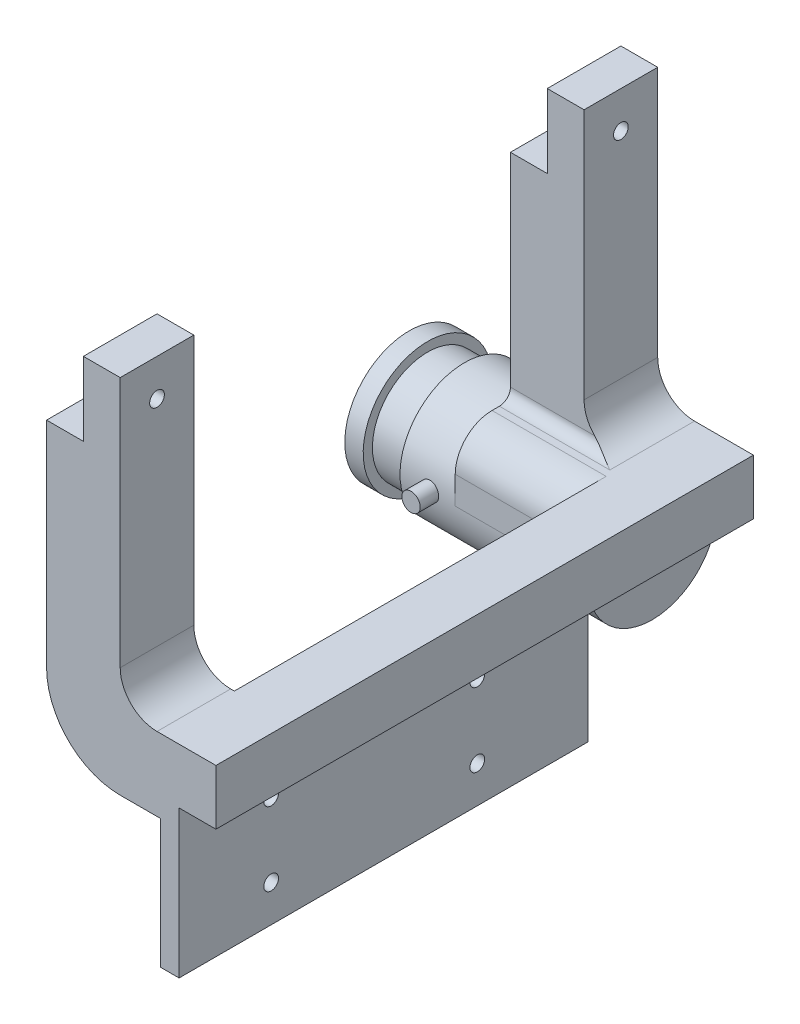
SolidWorks part; units mm, degrees
ref_plane "Front Plane" through (0, 0, 0) normal (0, 0, 1) x (1, 0, 0)
ref_plane "Top Plane" through (0, 0, 0) normal (0, 1, 0) x (1, 0, 0)
ref_plane "Right Plane" through (0, 0, 0) normal (1, 0, 0) x (0, 0, -1)
sketch "Sketch4" plane through (0, 0, 0) normal (1, 0, 0) x (0, 0, -1)
  line L0 (0, 10) -> (-10, 10)
  line L1 (0, 0) -> (126, 0)
  line L2 (0, 0) -> (0, 10)
  line L3 (0, 10) -> (126, 10) construction
  line L4 (126, 0) -> (126, 10)
  line L5 (-10, 10) -> (-10, 25)
  line L6 (-10, 25) -> (136, 25)
  line L7 (136, 25) -> (136, 10)
  line L8 (136, 10) -> (126, 10)
  dimension "D1" = 10
  dimension "D2" = 126
  dimension "D3" = 10
  dimension "D4" = 10
  dimension "D5" = 15
extrude "Boss-Extrude3" add sketch "Sketch4" along normal blind 10
sketch "Sketch8" plane through (0, 0, 0) normal (-1, 0, 0) x (0, 0, 1)
  line L1 (-136, 25) -> (10, 25)
  line L2 (-136, 25) -> (-136, 10)
  line L3 (-136, 10) -> (10, 10)
  line L4 (10, 25) -> (10, 10)
extrude "Boss-Extrude6" add sketch "Sketch8" along normal blind 5
sketch "Sketch9" plane through (0, 10, 0) normal (0, -1, 0) x (1, 0, 0)
  line L0 (10, -136) -> (-5, -136) construction
  line L1 (-5, 10) -> (0, 10)
  line L2 (-5, 10) -> (-5, -136)
  line L3 (-5, -136) -> (0, -136)
  line L4 (0, 10) -> (0, -136)
extrude "Boss-Extrude7" add sketch "Sketch9" along normal blind 20
sketch "Sketch10" plane through (0, 0, 0) normal (1, 0, 0) x (0, 0, -1)
  line L0 (0, 0) -> (0, -10) construction
  line L1 (136, -10) -> (-10, -10) construction
  line L2 (126, 0) -> (126, -10) construction
  line L3 (43, 0) -> (43, -10) construction
  line L5 (-10, -10) -> (-10, 10) construction
  circle A0 centre (15, -5) radius 2
  circle A1 centre (71, -5) radius 2
  dimension "D2" = 4
  dimension "D1" = 15
  dimension "D3" = 53
extrude "Cut-Extrude2" [suppressed] cut sketch "Sketch10" against normal blind 20
sketch "Sketch5" plane through (10, 0, 0) normal (1, 0, 0) x (0, 0, -1)
  line L0 (266, 95.52) -> (266, 25) construction
  line L1 (136, 10) -> (266, 10)
  line L2 (136, 10) -> (136, 25)
  line L3 (136, 25) -> (261, 25)
  line L4 (266, 10) -> (266, 25) construction
  line L5 (266, 10) -> (276, 10)
  line L6 (266, 10) -> (266, 95.52) construction
  line L7 (266, 95.52) -> (281, 95.52) construction
  line L8 (281, 10) -> (281, 95.52) construction
  line L9 (266, 84.1664) -> (266, 30)
  line L10 (281, 84.1664) -> (281, 15)
  circle A0 centre (273.5, 102.02) radius 6.5
  arc A1 (263, 91.3079) -> (284, 91.3079) centre (273.5, 102.02) cw
  arc A2 (284, 91.3079) -> (281, 84.1664) centre (291, 84.1664) ccw
  arc A3 (263, 91.3079) -> (266, 84.1664) centre (256, 84.1664) cw
  arc A4 (276, 10) -> (281, 15) centre (276, 15) ccw
  arc A5 (261, 25) -> (266, 30) centre (261, 30) ccw
  point P14 (281, 89.0296)
  point P17 (266, 89.0296)
  dimension "D5" = 13
  dimension "D6" = 15
  dimension "D7" = 10
  dimension "D8" = 5
  dimension "D1" = 130
  dimension "D2" = 15
  dimension "D3" = 15
  dimension "D4" = 85.52
  dimension "D9" = 7.5
extrude "Boss-Extrude4" [suppressed] add sketch "Sketch5" against normal blind 15
sketch "Sketch6" [suppressed] plane through (-5, 0, 0) normal (-1, 0, 0) x (0, 0, 1)
  circle A0 centre (-273.5, 102.02) radius 6.5
  circle A1 centre (-273.5, 102.02) radius 15
extrude "Boss-Extrude5" [suppressed] add sketch "Sketch6" along normal blind 50
ref_plane "Plane2" [suppressed] through (0, 0, -288.5) normal (0, 0, -1) x (-1, 0, 0)
ref_plane "Plane3" [suppressed] through (0, 0, -258.5) normal (0, 0, 1) x (1, 0, 0)
sketch "Sketch7" [suppressed] plane through (0, 0, -288.5) normal (0, 0, -1) x (-1, 0, 0)
  line L0 (-10, 117.02) -> (-10, 91.3079) construction
  circle A0 centre (20, 102.02) radius 2
  circle A1 centre (0, 102.02) radius 2
  dimension "D1" = 4
  dimension "D2" = 4
  dimension "D3" = 10
  dimension "D4" = 20
extrude "Cut-Extrude1" [suppressed] cut sketch "Sketch7" against normal blind 50
sketch "Sketch13" [suppressed] plane through (-5, 0, 0) normal (-1, 0, 0) x (0, 0, 1)
  line L0 (-196, 25) -> (-196, 10) construction
  line L1 (-136, 10) -> (-276, 10) construction
  line L2 (-136, 25) -> (-136, 10) construction
  circle A0 centre (-190, 17.5) radius 2
  circle A1 centre (-142, 17.5) radius 2
  dimension "D2" = 4
  dimension "D3" = 4
  dimension "D1" = 6
  dimension "D4" = 6
extrude "Cut-Extrude3" [suppressed] cut sketch "Sketch13" against normal blind 20
sketch "Sketch12" [suppressed] plane through (0, 25, 0) normal (0, 1, 0) x (1, 0, 0)
  line L0 (-5, 136) -> (10, 136) construction
  line L1 (-5, -10) -> (-5, 261) construction
  line L2 (10, 261) -> (10, -10) construction
  line L3 (10, -10) -> (-5, -10) construction
  line L4 (-5, 196) -> (10, 196) construction
  line L5 (2.5, 196) -> (2.5, 136)
  line L6 (2.5, 196) -> (-5, 196)
  line L7 (2.5, 136) -> (10, 136)
  dimension "D1" = 146
  dimension "D2" = 60
split "Split2" [suppressed] bodies to split 112
sketch "Sketch14" plane through (0, 0, 10) normal (0, 0, 1) x (1, 0, 0)
  line L0 (-5, 25) -> (-6, 25)
  line L1 (-16, 35) -> (-16, 83.24)
  line L2 (-16, 83.24) -> (-36, 83.24) construction
  line L3 (-36, 83.24) -> (-36, 25)
  line L4 (-16, 5) -> (-5, 5)
  line L5 (-5, -10) -> (-5, 25) construction
  line L6 (-5, 5) -> (-5, 25)
  line L8 (10, 25) -> (-5, 25) construction
  line L9 (-36, 83.24) -> (-36, 93.24)
  line L10 (-36, 93.24) -> (-36, 103.24)
  line L11 (-36, 103.24) -> (-16, 103.24)
  line L12 (-16, 103.24) -> (-16, 83.24)
  arc A0 (-6, 25) -> (-16, 35) centre (-6, 35) cw
  arc A1 (-36, 25) -> (-16, 5) centre (-16, 25) ccw
  point P16 (-16, 25)
  point P19 (-36, 5)
  dimension "D7" = 10
  dimension "D8" = 20
  dimension "D1" = 20
  dimension "D2" = 20
  dimension "D3" = 78.24
  dimension "D4" = 10
  dimension "D5" = 10
  dimension "D6" = 11
ref_plane "Plane4" through (0, 0, -63) normal (0, 0, 1) x (1, 0, 0)
extrude "Boss-Extrude8" add sketch "Sketch14" against normal blind 20
sketch "Sketch17" plane through (-36, 0, 0) normal (-1, 0, 0) x (0, 0, 1)
  line L0 (10, 103.24) -> (10, 25) construction
  line L1 (-10, 103.24) -> (10, 103.24)
  line L2 (-10, 103.24) -> (-10, 83.24)
  line L3 (-10, 83.24) -> (10, 83.24)
  line L4 (10, 103.24) -> (10, 83.24)
  dimension "D1" = 20
extrude "Cut-Extrude4" cut sketch "Sketch17" against normal blind 10
sketch "Sketch18" plane through (-26, 0, 0) normal (-1, 0, 0) x (0, 0, 1)
  line L0 (10, 103.24) -> (-10, 103.24) construction
  circle A0 centre (0, 93.24) radius 2
  dimension "D1" = 4
  dimension "D2" = 10
extrude "Cut-Extrude5" cut sketch "Sketch18" against normal up to next (10 mm away)
mirror "Mirror2" about plane through (0, 0, -63) normal (0, 0, 1) of "Cut-Extrude5", "Cut-Extrude4", "Boss-Extrude8"
sketch "Sketch20" plane through (-36, 0, 0) normal (-1, 0, 0) x (0, 0, 1)
  line L0 (10, -10) -> (-136, -10) construction
  line L1 (-136, 25) -> (-101, 25)
  line L2 (-136, 25) -> (-136, -10)
  line L3 (-136, -10) -> (-101, -10)
  line L4 (-101, 25) -> (-101, -10)
  dimension "D1" = 35
  dimension "D2" = 35
extrude "Boss-Extrude9" add sketch "Sketch20" against normal up to surface (31 mm away) up to face at (-5, 6.25, -63)
sketch "Sketch21" plane through (-36, 0, 0) normal (-1, 0, 0) x (0, 0, 1)
  line L0 (-101, 25) -> (-136, -10) construction
  line L2 (-116, 25) -> (-136, 25) construction
  line L5 (-136, 83.24) -> (-136, -10) construction
  line L10 (-136, 25) -> (-101, -10) construction
  circle A8 centre (-118.5, 7.5) radius 17.5
extrude "Boss-Extrude10" add sketch "Sketch21" along normal blind 30
sketch "Sketch22" plane through (-36, 0, 0) normal (-1, 0, 0) x (0, 0, 1)
  line L0 (-101, 25) -> (-136, -10) construction
  line L1 (-101, -10) -> (-136, 25) construction
  line L2 (-136, 83.24) -> (-136, 7.5) construction
  line L3 (-101, 25) -> (-101, -10) construction
  line L4 (-136, 7.5) -> (-136, -14.7774)
  line L5 (-136, -14.7774) -> (-101, -14.7774)
  line L6 (-101, -14.7774) -> (-101, 7.5)
  arc A0 (-136, 7.5) -> (-101, 7.5) centre (-118.5, 7.5) ccw
extrude "Cut-Extrude6" cut sketch "Sketch22" against normal up to surface (31 mm away) up to face at (-5, 6.6667, -33.6667)
fillet "Fillet1" radius 3 1 edges at (-21, 25, -116)
ref_plane "Plane5" through (0, 25, 0) normal (0, 1, 0) x (1, 0, 0)
sketch "Sketch23" plane through (0, 25, 0) normal (0, 1, 0) x (1, 0, 0)
  line L0 (-66, 118.5) -> (-36, 118.5) construction
  line L1 (-66, 136) -> (-66, 101) construction
  line L2 (-36, 136) -> (-36, 101) construction
  line L3 (-45.5, 118.5) -> (-40.5, 118.5) construction
  line L4 (-45.5, 121) -> (-40.5, 121)
  line L5 (-45.5, 116) -> (-40.5, 116)
  circle A0 centre (-43, 118.5) radius 2.5 construction
  arc A1 (-45.5, 121) -> (-45.5, 116) centre (-45.5, 118.5) ccw
  arc A2 (-40.5, 116) -> (-40.5, 121) centre (-40.5, 118.5) ccw
  point P10 (-43, 118.5)
  dimension "D2" = 5
  dimension "D4" = 2.5
  dimension "D1" = 7
  dimension "D3" = 5
extrude "Cut-Extrude7" [suppressed] cut sketch "Sketch23" against normal up to next
ref_plane "Plane6" through (0, 0, -101) normal (0, 0, 1) x (1, 0, 0)
sketch "Sketch25" plane through (0, 0, -101) normal (0, 0, 1) x (1, 0, 0)
  line L0 (-66, 7.5) -> (-36, 7.5) construction
  line L1 (-66, 25) -> (-66, -10) construction
  line L2 (-45.5, 7.5) -> (-40.5, 7.5) construction
  line L3 (-45.5, 10) -> (-40.5, 10)
  line L4 (-45.5, 5) -> (-40.5, 5)
  circle A0 centre (-43, 7.5) radius 2.5 construction
  arc A1 (-45.5, 10) -> (-45.5, 5) centre (-45.5, 7.5) ccw
  arc A2 (-40.5, 5) -> (-40.5, 10) centre (-40.5, 7.5) ccw
  point P9 (-43, 7.5)
  dimension "D1" = 5
  dimension "D4" = 2.5
  dimension "D2" = 7
  dimension "D3" = 5
extrude "Cut-Extrude8" [suppressed] cut sketch "Sketch25" against normal through all
ref_plane "Plane7" through (-51, 0, 0) normal (-1, 0, 0) x (0, 0, 1)
sketch "Sketch26" plane through (-51, 0, 0) normal (-1, 0, 0) x (0, 0, 1)
  arc A0 (-101, 7.5) -> (-136, 7.5) centre (-118.5, 7.5) ccw construction
  arc A1 (-101, 7.5) -> (-136, 7.5) centre (-118.5, 7.5) ccw construction
  circle A2 centre (-118.5, 7.5) radius 15
  circle A3 centre (-118.5, 7.5) radius 17.5
  dimension "D1" = 30
extrude "Cut-Extrude9" cut sketch "Sketch26" along normal blind 10
fillet "Fillet2" radius 10 1 edges at (-20.5, 25, -101)
sketch "Sketch27" plane through (0, -10, 0) normal (0, -1, 0) x (1, 0, 0)
  line L1 (-5, 10) -> (0, 10)
  line L2 (-5, 10) -> (-5, -136)
  line L3 (-5, -136) -> (0, -136)
  line L4 (0, 10) -> (0, -136)
extrude "Boss-Extrude11" add sketch "Sketch27" along normal blind 20
sketch "Sketch28" plane through (0, 0, 0) normal (0, -1, 0) x (1, 0, 0)
  line L1 (10, 0) -> (0, 0)
  line L2 (10, 0) -> (10, -126)
  line L3 (10, -126) -> (0, -126)
  line L4 (0, 0) -> (0, -126)
extrude "Cut-Extrude10" cut sketch "Sketch28" against normal up to surface (10 mm away) up to face at (5, 10, 5)
sketch "Sketch29" plane through (-5, 0, 0) normal (-1, 0, 0) x (0, 0, 1)
  line L0 (10, -30) -> (10, 5) construction
  line L1 (10, -30) -> (-136, -30) construction
  circle A0 centre (-15, -20) radius 2
  circle A1 centre (-71, -20) radius 2
  circle A2 centre (-15, 0) radius 2
  circle A3 centre (-71, 0) radius 2
  dimension "D1" = 4
  dimension "D5" = 4
  dimension "D2" = 25
  dimension "D3" = 10
  dimension "D4" = 56
  dimension "D6" = 2
extrude "Cut-Extrude11" cut sketch "Sketch29" against normal up to surface (5 mm away) up to face at (0, -10, -63)
sketch "Sketch30" plane through (-5, 0, 0) normal (-1, 0, 0) x (0, 0, 1)
  line L0 (-136, 83.24) -> (-136, 7.5) construction
  line L1 (-136, 7.5) -> (-136, -30)
  line L2 (-136, -30) -> (-101, -30)
  line L3 (10, -30) -> (-136, -30) construction
  line L4 (-101, -30) -> (-101, 7.5)
  arc A0 (-136, 7.5) -> (-101, 7.5) centre (-118.5, 7.5) ccw
  arc A1 (-101, 7.5) -> (-136, 7.5) centre (-118.5, 7.5) ccw construction
  arc A2 (-136, 7.5) -> (-101, 7.5) centre (-118.5, 7.5) ccw construction
extrude "Cut-Extrude12" cut sketch "Sketch30" against normal up to surface (5 mm away) up to face at (0, -20, -69)
sketch "Sketch31" plane through (0, 0, -101) normal (0, 0, 1) x (1, 0, 0)
  circle A0 centre (-43, 7.5) radius 2.5
  dimension "D2" = 5
  dimension "D1" = 7
extrude "Boss-Extrude12" add sketch "Sketch31" along normal blind 5 and the other way up to surface separate body contours A0
